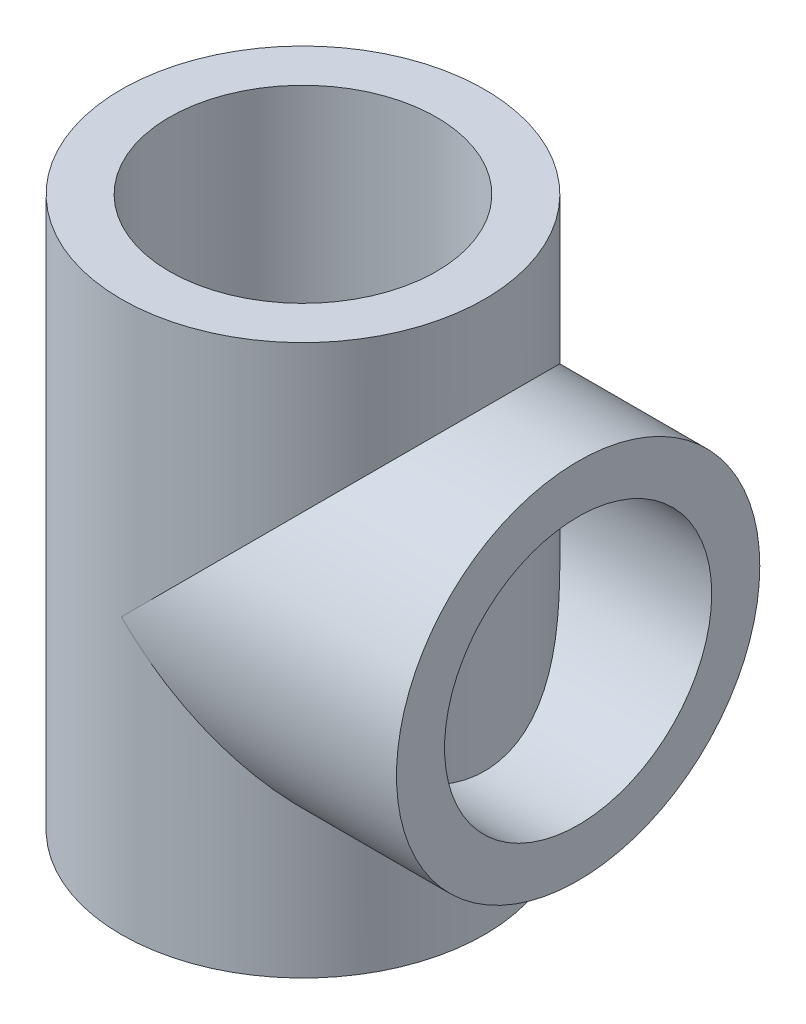
SolidWorks part; units mm, degrees
ref_plane "Front Plane" through (0, 0, 0) normal (0, 0, 1) x (1, 0, 0)
ref_plane "Top Plane" through (0, 0, 0) normal (0, 1, 0) x (1, 0, 0)
ref_plane "Right Plane" through (0, 0, 0) normal (1, 0, 0) x (0, 0, -1)
sketch "Sketch1" plane through (0, 0, 0) normal (0, 1, 0) x (1, 0, 0)
  circle A0 centre (0, 0) radius 25
  circle A1 centre (0, 0) radius 34
  dimension "D1" = 50
  dimension "D3" = 68
  dimension "D2" = 9
extrude "Boss-Extrude1" add sketch "Sketch1" along normal mid plane 103
ref_plane "Plane1" through (51.5, 0, 0) normal (1, 0, 0) x (0, 0, -1)
sketch "Sketch2" plane through (51.5, 0, 0) normal (1, 0, 0) x (0, 0, -1)
  circle A0 centre (0, 0) radius 34
  circle A1 centre (0, 0) radius 25
  dimension "D2" = 50
  dimension "D1" = 9
extrude "Boss-Extrude2" add sketch "Sketch2" against normal up to surface (51.5 mm away) up to face at (0, 51.5, 34)
